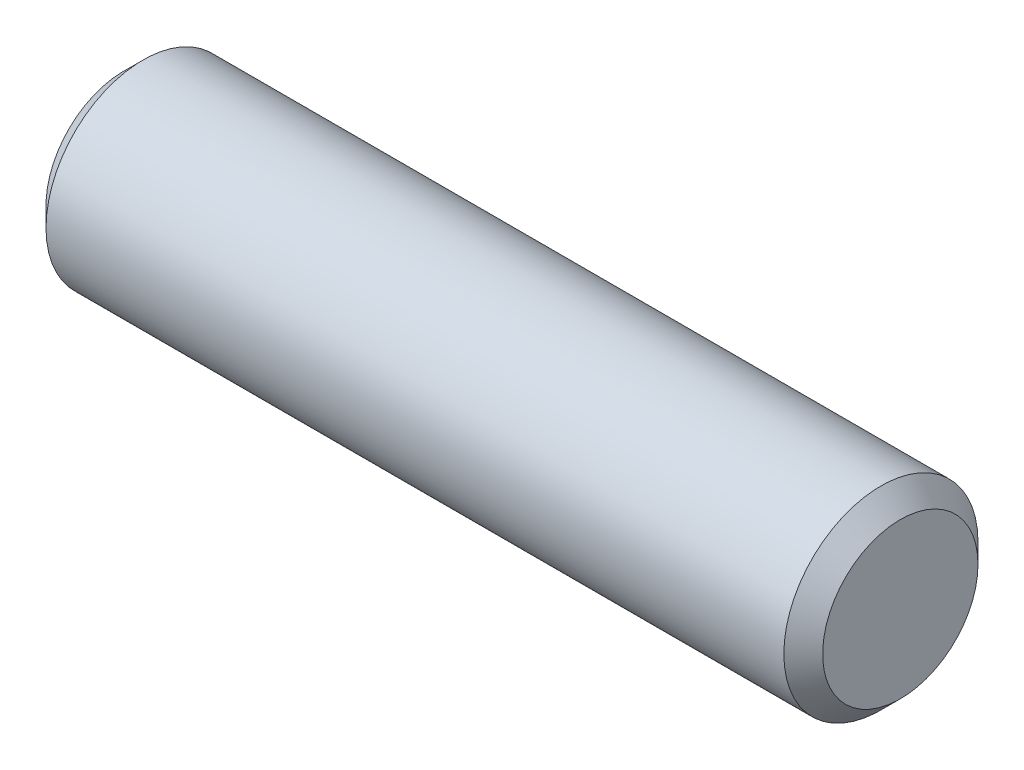
SolidWorks part; units mm, degrees
ref_plane "Front" through (0, 0, 0) normal (0, 0, 1) x (1, 0, 0)
ref_plane "Top" through (0, 0, 0) normal (0, 1, 0) x (1, 0, 0)
ref_plane "Right" through (0, 0, 0) normal (1, 0, 0) x (0, 0, -1)
sketch "Sketch1" plane through (0, 0, 0) normal (0, 0, 1) x (1, 0, 0)
  line L0 (-12.7, 0) -> (12.7, 0) construction
  line L1 (12.7, 3.175) -> (12.7, -3.175) construction
  line L2 (-12.7, 3.175) -> (-12.7, -3.175) construction
  dimension "Length" = 25.4
  dimension "Diameter" = 6.35
sketch "Sketch2" plane through (0, 0, 0) normal (1, 0, 0) x (0, 0, -1)
  circle A0 centre (0, 0) radius 3.175
extrude "Extrude1" add sketch "Sketch2" against normal up to vertex (12.7 mm away) and the other way up to vertex (12.7 mm away) up to point (-12.7, 3.175, 0) other way up to point (12.7, 3.175, 0)
chamfer "Chamfer1" distance 0.635 angle 45 2 edges at (12.7, 0, -3.175) (-12.7, 0, -3.175)
equation "\"D1@Chamfer1\" = \"Diameter@Sketch1\"*.1"
